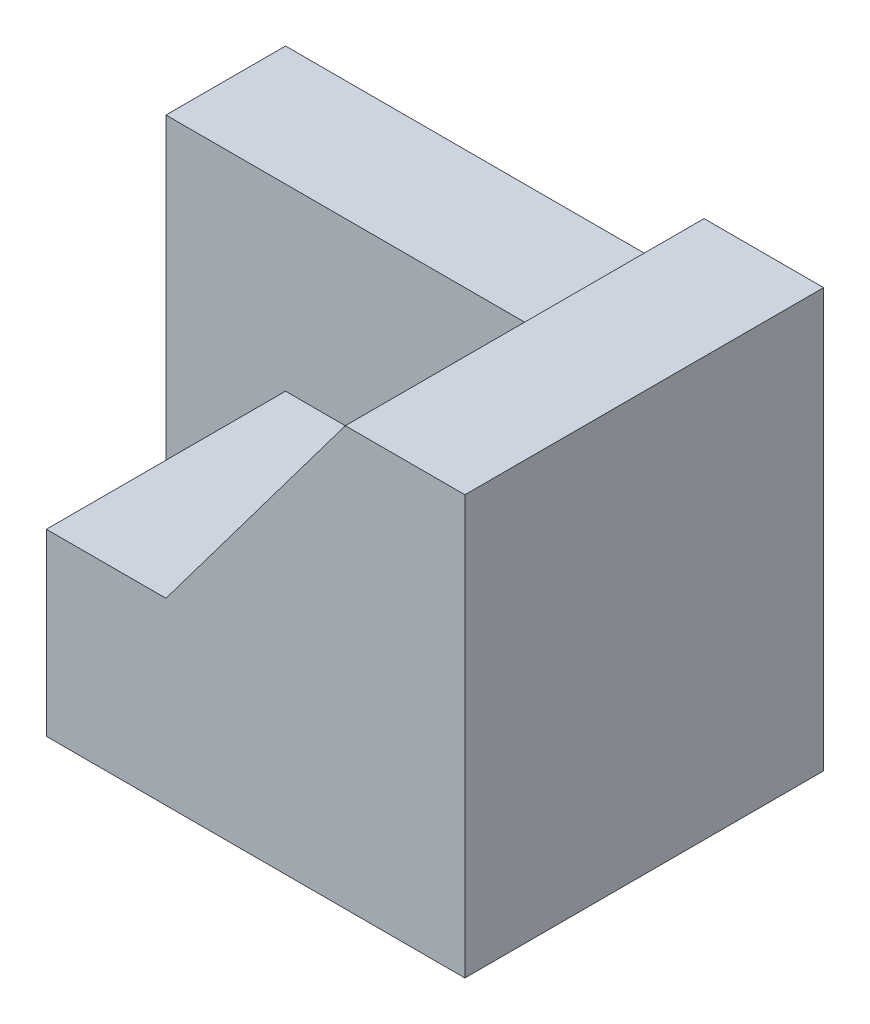
SolidWorks part; units mm, degrees
ref_plane "Front Plane" through (0, 0, 0) normal (0, 0, 1) x (1, 0, 0)
ref_plane "Top Plane" through (0, 0, 0) normal (0, 1, 0) x (1, 0, 0)
ref_plane "Right Plane" through (0, 0, 0) normal (1, 0, 0) x (0, 0, -1)
sketch "Sketch1" plane through (0, 0, 0) normal (0, 0, 1) x (1, 0, 0)
  line L1 (0, 0) -> (90, 0)
  line L2 (0, 0) -> (0, 60)
  line L3 (0, 60) -> (90, 60)
  line L4 (90, 0) -> (90, 60)
  dimension "D1" = 90
  dimension "D2" = 60
extrude "Boss-Extrude1" add sketch "Sketch1" along normal blind 20
sketch "Sketch2" plane through (0, 0, 0) normal (0, 0, 1) x (1, 0, 0)
  line L0 (20, 0) -> (20, 30)
  line L1 (0, 0) -> (90, 0) construction
  line L2 (20, 30) -> (40, 30)
  line L3 (40, 30) -> (70, 70)
  line L4 (70, 70) -> (90, 70)
  line L5 (90, 70) -> (90, 0)
  line L6 (90, 0) -> (20, 0)
  dimension "D1" = 30
  dimension "D2" = 20
  dimension "D3" = 20
  dimension "D4" = 30
  dimension "D5" = 70
extrude "Boss-Extrude2" add sketch "Sketch2" along normal blind 60
